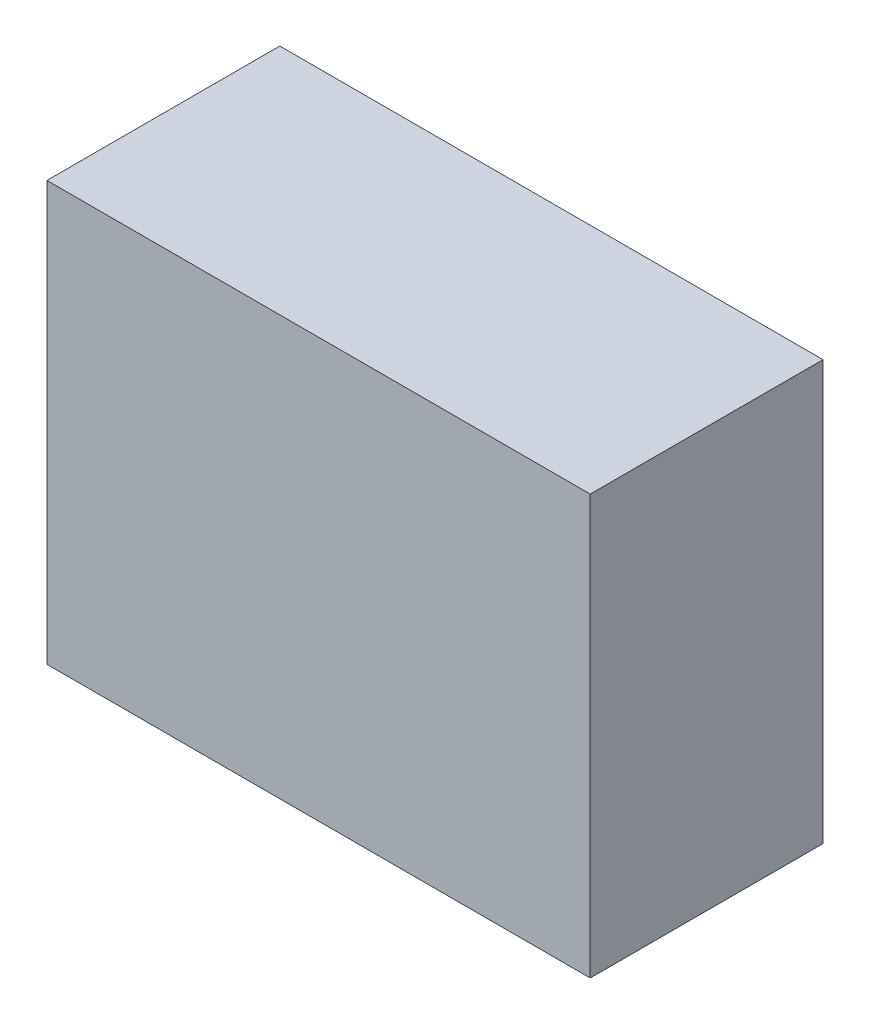
SolidWorks part; units mm, degrees
ref_plane "Front Plane" through (0, 0, 0) normal (0, 0, 1) x (1, 0, 0)
ref_plane "Top Plane" through (0, 0, 0) normal (0, 1, 0) x (1, 0, 0)
ref_plane "Right Plane" through (0, 0, 0) normal (1, 0, 0) x (0, 0, -1)
sketch "Sketch1" plane through (0, 0, 0) normal (0, 0, 1) x (1, 0, 0)
  line L1 (0, 0) -> (70, 0)
  line L2 (0, 0) -> (0, 54)
  line L3 (0, 54) -> (70, 54)
  line L4 (70, 0) -> (70, 54)
  dimension "D1" = 70
  dimension "D2" = 54
extrude "Boss-Extrude1" add sketch "Sketch1" along normal blind 30
